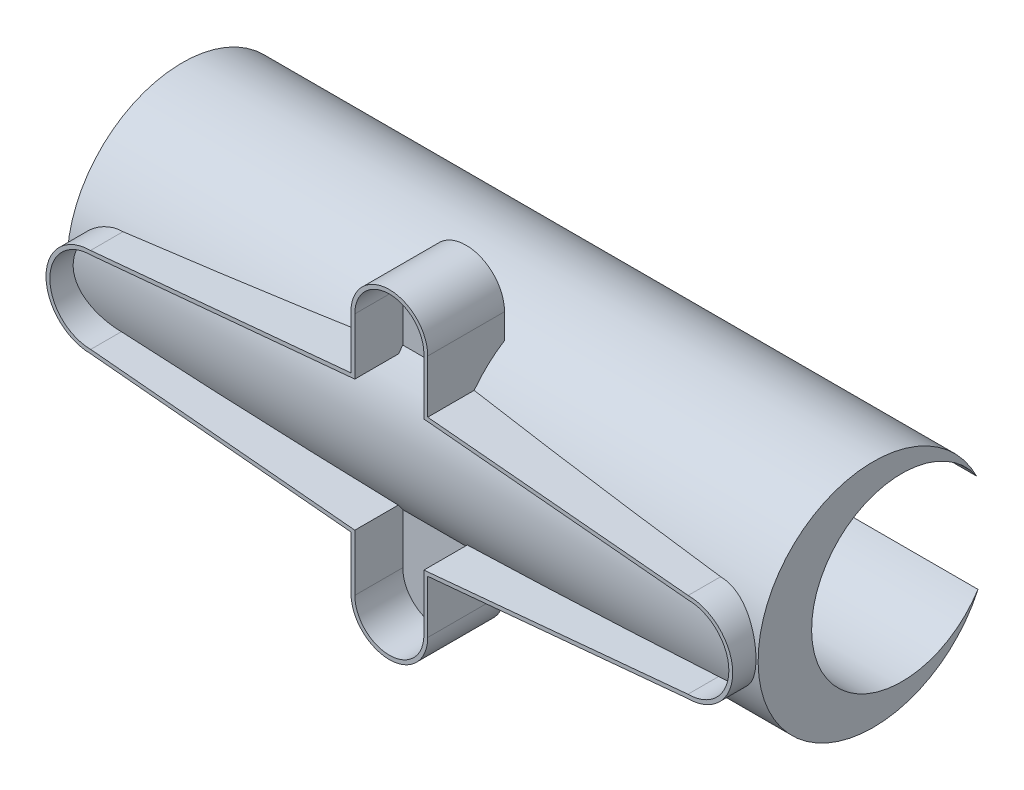
SolidWorks part; units mm, degrees
ref_plane "Front Plane" through (0, 0, 0) normal (0, 0, 1) x (1, 0, 0)
ref_plane "Top Plane" through (0, 0, 0) normal (0, 1, 0) x (1, 0, 0)
ref_plane "Right Plane" through (0, 0, 0) normal (1, 0, 0) x (0, 0, -1)
sketch "Sketch1" plane through (0, 0, 0) normal (0, 0, 1) x (1, 0, 0)
  line L12 (-23.2333, 11.837) -> (-36.8011, 10.5771)
  line L13 (-36.8011, 5.9166) -> (-23.2333, 4.6567)
  line L14 (-23.2333, 4.6567) -> (-23.2333, 1.8969)
  line L15 (-19.2333, 1.8969) -> (-19.2333, 4.6567)
  line L16 (-19.2333, 4.6567) -> (-5.6654, 5.9166)
  line L17 (-5.6654, 10.5771) -> (-19.2333, 11.837)
  line L18 (-19.2333, 11.837) -> (-19.2333, 14.5969)
  line L19 (-23.2333, 14.5969) -> (-23.2333, 11.837)
  arc A4 (-36.8011, 10.5771) -> (-36.8011, 5.9166) centre (-36.7916, 8.2469) ccw
  arc A5 (-23.2333, 1.8969) -> (-19.2333, 1.8969) centre (-21.2333, 1.8969) ccw
  arc A6 (-5.6654, 5.9166) -> (-5.6654, 10.5771) centre (-5.6749, 8.2469) ccw
  arc A7 (-19.2333, 14.5969) -> (-23.2333, 14.5969) centre (-21.2333, 14.5969) ccw
extrude "Boss-Extrude3" add sketch "Sketch1" along normal blind 4
sketch "Sketch4" plane through (0, 0, 4) normal (0, 0, 1) x (1, 0, 0)
  line L0 (-23.0333, 11.6547) -> (-36.7916, 10.3771)
  line L1 (-36.7916, 6.1166) -> (-23.0333, 4.839)
  line L2 (-23.0333, 4.839) -> (-23.0333, 1.8969)
  line L3 (-19.4333, 1.8969) -> (-19.4333, 4.839)
  line L4 (-19.4333, 4.839) -> (-5.6749, 6.1166)
  line L5 (-5.6749, 10.3771) -> (-19.4333, 11.6547)
  line L6 (-19.4333, 11.6547) -> (-19.4333, 14.5969)
  line L7 (-23.0333, 14.5969) -> (-23.0333, 11.6547)
  arc A0 (-19.4333, 14.5969) -> (-23.0333, 14.5969) centre (-21.2333, 14.5969) ccw
  arc A1 (-5.6749, 6.1166) -> (-5.6749, 10.3771) centre (-5.6749, 8.2469) ccw
  arc A2 (-23.0333, 1.8969) -> (-19.4333, 1.8969) centre (-21.2333, 1.8969) ccw
  arc A3 (-36.7916, 10.3771) -> (-36.7916, 6.1166) centre (-36.7916, 8.2469) ccw
extrude "Cut-Extrude1" cut sketch "Sketch4" against normal blind 2.5
sketch "Sketch6" plane through (-19.2333, 0, 0) normal (1, 0, 0) x (0, 0, -1)
  arc A0 (8.5958, 10.8794) -> (8.6694, 5.7335) centre (4.7, 8.2502) ccw
  arc A1 (8.5958, 10.8794) -> (8.6694, 5.7335) centre (3.213, 8.229) ccw
extrude "Boss-Extrude4" add sketch "Sketch6" along normal blind 16 and the other way blind 20
